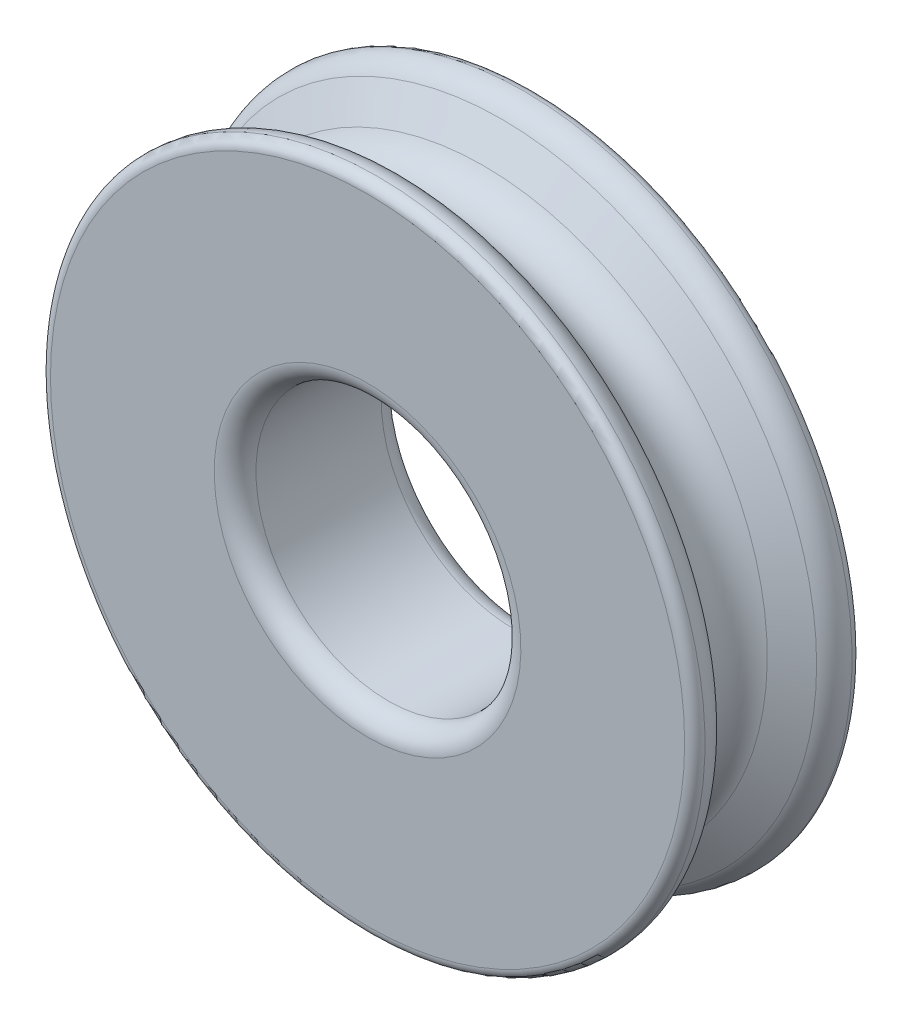
SolidWorks part; units mm, degrees
ref_plane "Front Plane" through (0, 0, 0) normal (0, 0, 1) x (1, 0, 0)
ref_plane "Top Plane" through (0, 0, 0) normal (0, 1, 0) x (1, 0, 0)
ref_plane "Right Plane" through (0, 0, 0) normal (1, 0, 0) x (0, 0, -1)
sketch "Sketch1" plane through (0, 0, 0) normal (1, 0, 0) x (0, 0, -1)
  line L0 (0, 0) -> (0, 17451.5356) construction
  line L1 (4, 0) -> (-4, 0)
  line L2 (-4, 0) -> (-4, 15.2006)
  line L3 (4, 0) -> (4, 15.2006)
  line L6 (-2.4257, 15.1015) -> (-1.5588, 13.6)
  line L7 (2.4257, 15.1015) -> (1.5588, 13.6)
  arc A0 (-4, 15.2006) -> (-3.525, 15.7) centre (-3.5, 15.2006) cw
  arc A1 (4, 15.2006) -> (3.525, 15.7) centre (3.5, 15.2006) ccw
  arc A2 (-3.525, 15.7) -> (-2.4257, 15.1015) centre (-3.465, 14.5015) cw
  arc A3 (3.525, 15.7) -> (2.4257, 15.1015) centre (3.465, 14.5015) ccw
  arc A4 (-1.5588, 13.6) -> (1.5588, 13.6) centre (0, 14.5) ccw
  point P6 (0, 0)
  point P18 (0, 12.7)
  dimension "D2" = 0.5
  dimension "D4" = 1.2
  dimension "D5" = 1.8
  dimension "D1" = 8
  dimension "D3" = 12.7
  dimension "D6" = 3
  dimension "D7" = 60
revolve "Revolve1" add sketch "Sketch1" angle 360 about L1
sketch "Sketch2" plane through (0, 0, 4) normal (0, 0, 1) x (1, 0, 0)
  circle A0 centre (0, 0) radius 6.35
  circle A1 centre (0, 0) radius 15.2006
  circle A2 centre (0, 0) radius 15.2006
  dimension "D2" = 12.7
  dimension "D1" = 0
extrude "Cut-Extrude2" cut sketch "Sketch2" against normal through all contours A0
fillet "Fillet3" radius 1 2 edges at (6.35, 0, -4) (6.35, 0, 4)
